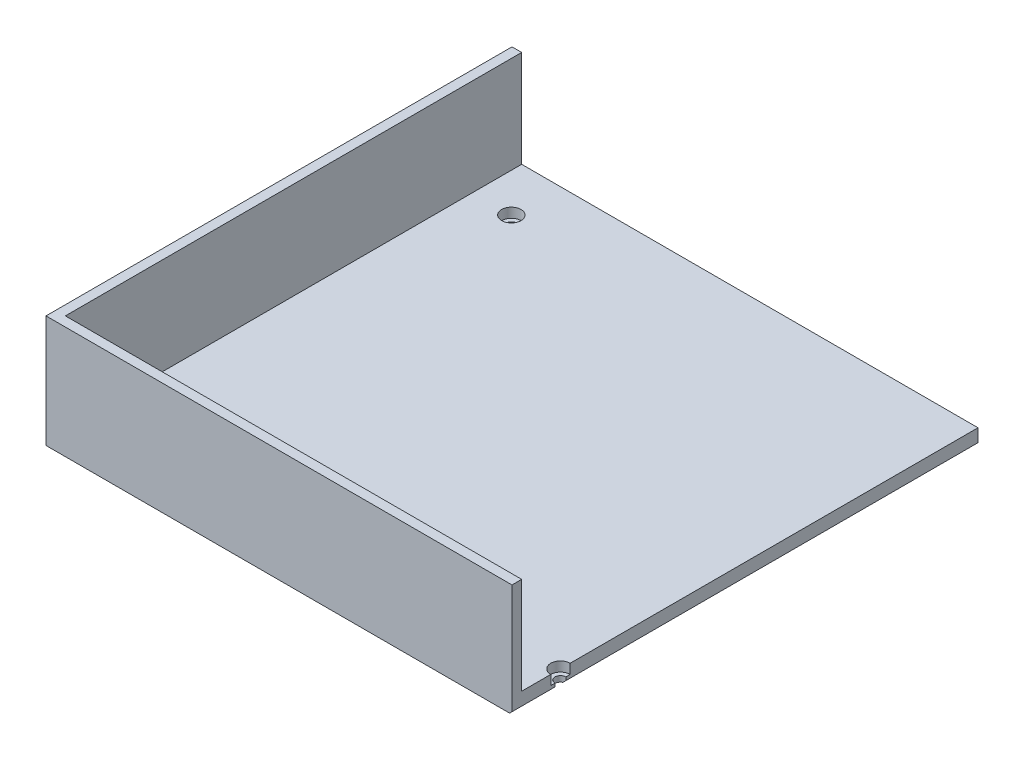
SolidWorks part; units mm, degrees
ref_plane "Front Plane" through (0, 0, 0) normal (0, 0, 1) x (1, 0, 0)
ref_plane "Top Plane" through (0, 0, 0) normal (0, 1, 0) x (1, 0, 0)
ref_plane "Right Plane" through (0, 0, 0) normal (1, 0, 0) x (0, 0, -1)
sketch "Sketch1" plane through (0, 0, 0) normal (0, 1, 0) x (1, 0, 0)
  line L1 (-96.2, 96.2) -> (96.2, 96.2)
  line L2 (-96.2, 96.2) -> (-96.2, -96.2)
  line L3 (-96.2, -96.2) -> (96.2, -96.2)
  line L4 (96.2, 96.2) -> (96.2, -96.2)
  line L5 (-96.2, 96.2) -> (96.2, -96.2) construction
  line L6 (-96.2, -96.2) -> (96.2, 96.2) construction
  point P0 (0, 0)
  dimension "D1" = 192.4
  dimension "D2" = 192.4
extrude "Boss-Extrude1" add sketch "Sketch1" along normal blind 6.35
sketch "Sketch2" plane through (0, 6.35, 0) normal (0, 1, 0) x (1, 0, 0)
  line L2 (-92.2, 92.2) -> (-92.2, -92.2)
  line L3 (-92.2, -92.2) -> (92.2, -92.2)
  line L4 (96.2, -96.2) -> (96.2, 96.2)
  line L5 (96.2, 96.2) -> (-96.2, 96.2)
  line L6 (-96.2, 96.2) -> (-96.2, -96.2)
  line L7 (-96.2, -96.2) -> (96.2, -96.2)
  line L10 (-96.2, 96.2) -> (-96.2, -96.2)
  line L11 (-96.2, -96.2) -> (96.2, -96.2)
  line L12 (92.2, 92.2) -> (-92.2, 92.2) construction
  line L13 (96.2, 96.2) -> (-96.2, 96.2) construction
  line L14 (92.2, -92.2) -> (92.2, 92.2) construction
  line L15 (96.2, -96.2) -> (96.2, 96.2) construction
  line L16 (-92.2, 92.2) -> (-92.2, 96.2)
  line L17 (96.2, 96.2) -> (-96.2, 96.2) construction
  line L18 (-92.2, 96.2) -> (-96.2, 96.2)
  line L19 (92.2, -92.2) -> (96.2, -92.2)
  line L20 (96.2, -96.2) -> (96.2, 96.2) construction
  line L21 (96.2, -92.2) -> (96.2, -96.2)
  dimension "D1" = 0
  dimension "D2" = 4
extrude "Boss-Extrude2" add sketch "Sketch2" along normal blind 40
sketch "Sketch3" plane through (0, 6.35, 0) normal (0, 1, 0) x (1, 0, 0)
  line L0 (-96.2, -96.2) -> (96.2, -96.2) construction
  line L1 (-96.2, 96.2) -> (-56.2, 96.2) construction
  line L2 (-96.2, 96.2) -> (-96.2, -96.2) construction
  line L3 (-96.2, -96.2) -> (-56.2, -96.2) construction
  line L4 (-56.2, 96.2) -> (-56.2, -96.2) construction
  line L5 (96.2, -92.2) -> (96.2, 96.2) construction
  line L6 (-96.2, 96.2) -> (96.2, 96.2) construction
  line L7 (-96.2, 96.2) -> (-96.2, 55.6473) construction
  line L8 (-96.2, 55.6473) -> (96.2, 55.6473) construction
  line L9 (96.2, 96.2) -> (96.2, 55.6473) construction
  line L10 (96.2, -76.2) -> (-96.2, -76.2) construction
  line L11 (-96.2, -96.2) -> (96.2, -96.2) construction
  line L12 (-96.2, -96.2) -> (-96.2, -56.2) construction
  line L13 (-96.2, -56.2) -> (96.2, -56.2) construction
  line L14 (96.2, -96.2) -> (96.2, -56.2) construction
  line L15 (-76.2, -96.2) -> (-76.2, 96.2) construction
  line L16 (96.2, 75.9237) -> (-96.2, 75.9237) construction
  circle A0 centre (-76.2, -76.2) radius 2.25
  circle A1 centre (-76.2, 75.9237) radius 2.25
  circle A2 centre (96.2, -76.2) radius 2.25
  point P15 (96.2, -76.2)
  point P21 (-76.2, -76.2)
  point P23 (-76.2, 75.9237)
  point P33 (96.2, -76.2)
  dimension "D4" = 4.5
  dimension "D1" = 40
  dimension "D2" = 40.5527
  dimension "D3" = 40
hole_wizard "CBORE for M4 SHCS1" positions "Sketch3" profile "Sketch4" counterbore size "M4" standard "ANSI Metric" end condition up to next
sketch "Sketch4" plane through (96.2, 6.35, 76.2) normal (1, 0, 0) x (0, 0, 1)
  line L0 (0, 0) -> (0, 6.35)
  line L1 (0, 6.35) -> (2.25, 6.35)
  line L3 (2.25, 6.35) -> (2.25, 4)
  line L4 (2.25, 4) -> (4, 4)
  line L5 (4, 4) -> (4, 0)
  line L7 (4, 0) -> (0, 0)
  line L11 (0, -6.35) -> (0, 107.95) construction
  dimension "Thru Hole Dia." = 4.5
  dimension "Thru Hole Depth" = 6.35
  dimension "C'Bore Dia." = 8
  dimension "C'Bore Depth" = 4
chamfer "Chamfer1" distance 1 angle 45 3 edges at (96.2, 0, 87.325) (0, 0, -96.2) (96.2, 0, -11.125)
mirror "Mirror1" [suppressed]
delete or keep bodies "Body-Delete/Keep 1" [suppressed] type delete bodies bodies 103
equation "\"D2@Sketch1\"=384.8/2"
